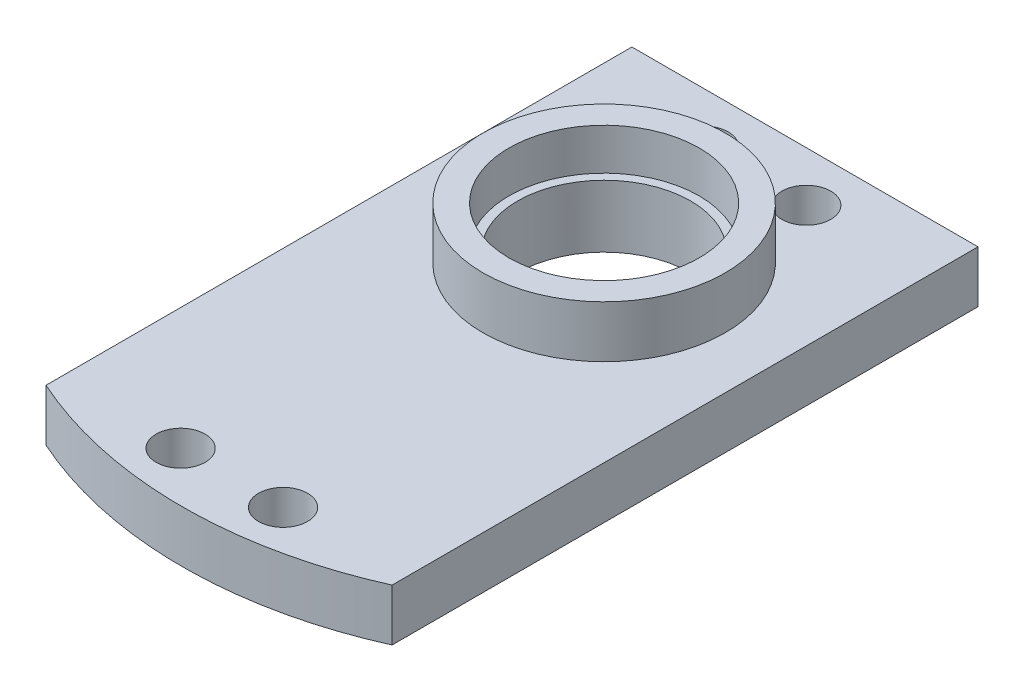
SolidWorks part; units mm, degrees
ref_plane "Front Plane" through (0, 0, 0) normal (0, 0, 1) x (1, 0, 0)
ref_plane "Top Plane" through (0, 0, 0) normal (0, 1, 0) x (1, 0, 0)
ref_plane "Right Plane" through (0, 0, 0) normal (1, 0, 0) x (0, 0, -1)
sketch "Sketch1" plane through (0, 0, 0) normal (0, 1, 0) x (1, 0, 0)
  line L1 (15.875, -28.575) -> (-15.875, -28.575)
  line L2 (15.875, -28.575) -> (15.875, 28.575)
  line L3 (15.875, 28.575) -> (-15.875, 28.575)
  line L4 (-15.875, -28.575) -> (-15.875, 28.575)
  line L5 (15.875, -28.575) -> (-15.875, 28.575) construction
  line L6 (15.875, 28.575) -> (-15.875, -28.575) construction
  point P0 (0, 0)
  dimension "D1" = 57.15
  dimension "D2" = 31.75
extrude "Boss-Extrude1" add sketch "Sketch1" along normal blind 4.7625
sketch "Sketch2" plane through (0, 4.7625, 0) normal (0, 1, 0) x (1, 0, 0)
  circle A0 centre (0, 10.15) radius 11.1125
  dimension "D1" = 22.225
  dimension "D2" = 10.15
extrude "Boss-Extrude2" add sketch "Sketch2" along normal blind 4.7625
sketch "Sketch3" plane through (0, 9.525, 0) normal (0, 1, 0) x (1, 0, 0)
  circle A0 centre (0, 10.15) radius 8.7312
  dimension "D1" = 17.4625
extrude "Cut-Extrude1" cut sketch "Sketch3" against normal blind 3.81 contours A0
sketch "Sketch4" plane through (0, 0, 0) normal (0, -1, 0) x (1, 0, 0)
  circle A0 centre (0, -10.15) radius 7.9375
  dimension "D1" = 15.875
extrude "Cut-Extrude2" cut sketch "Sketch4" against normal blind 7.9375
hole_wizard "#8 Clearance Hole2" positions "Sketch5" profile "Sketch7" hole size "#8" standard "ANSI Inch" end condition through all
sketch "Sketch5" plane through (0, 0, 0) normal (0, -1, 0) x (-1, 0, 0)
  line L1 (4.7, -24) -> (-4.7, -24)
  line L2 (4.7, -24) -> (4.7, 24)
  line L3 (4.7, 24) -> (-4.7, 24)
  line L4 (-4.7, -24) -> (-4.7, 24)
  line L5 (4.7, -24) -> (-4.7, 24) construction
  line L6 (4.7, 24) -> (-4.7, -24) construction
  circle A0 centre (0, 10.15) radius 8.7312 construction
  circle A1 centre (0, 10.15) radius 8.7312 construction
  point P2 (-4.7, 24)
  point P13 (4.7, -24)
  point P14 (4.7, 24)
  point P15 (-4.7, -24)
  point P18 (0, 0)
  dimension "D1" = 48
  dimension "D2" = 9.4
  dimension "D3" = 13.85
sketch "Sketch7" plane through (4.7, 0, -24) normal (1, 0, 0) x (0, 0, -1)
  line L0 (0, 0) -> (0, 9.525)
  line L1 (0, 9.525) -> (2.2479, 9.525)
  line L2 (2.2479, 9.525) -> (2.2479, 0)
  line L5 (2.2479, 0) -> (0, 0)
  line L11 (0, -6.35) -> (0, 107.95) construction
  dimension "Thru Hole Dia." = 4.4958
  dimension "Thru Hole Depth" = 9.525
sketch "Sketch8" plane through (0, 4.7625, 0) normal (0, 1, 0) x (1, 0, 0)
  line L4 (-15.875, 28.575) -> (-15.875, -28.575)
  line L5 (-15.875, -28.575) -> (15.875, -28.575)
  line L6 (15.875, -28.575) -> (15.875, 28.575)
  line L7 (15.875, 28.575) -> (-15.875, 28.575)
  line L8 (-15.875, -25.1715) -> (-15.875, -28.575)
  line L9 (-15.875, -28.575) -> (15.875, -28.575)
  line L10 (15.875, -28.575) -> (15.875, -25.1715)
  arc A0 (-15.875, -25.1715) -> (15.875, -25.1715) centre (0, 10.15) ccw
  line M12 (-15.875, 28.575) -> (-15.875, -28.575)
  line M13 (-15.875, -28.575) -> (15.875, -28.575)
  line M14 (15.875, -28.575) -> (15.875, 28.575)
  dimension "D1" = 0
extrude "Cut-Extrude3" cut sketch "Sketch8" against normal through all contours A0 L9 M14 | A0 M12 M13
